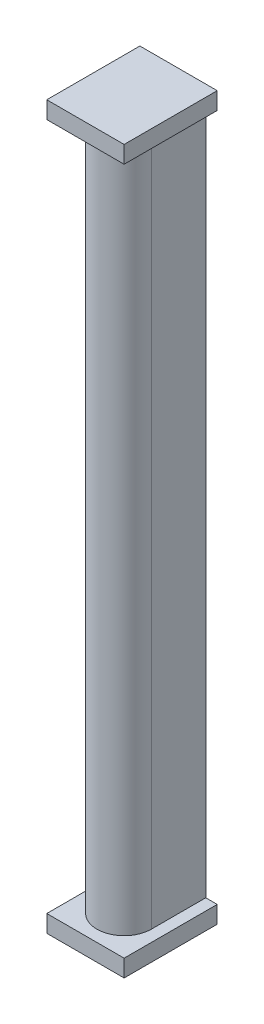
SolidWorks part; units mm, degrees
ref_plane "Front Plane" through (0, 0, 0) normal (0, 0, 1) x (1, 0, 0)
ref_plane "Top Plane" through (0, 0, 0) normal (0, 1, 0) x (1, 0, 0)
ref_plane "Right Plane" through (0, 0, 0) normal (1, 0, 0) x (0, 0, -1)
sketch "Sketch5" plane through (0, 0, 0) normal (0, 1, 0) x (1, 0, 0)
  line L1 (0, 0) -> (9.5, 0)
  line L2 (0, 0) -> (0, -9.5)
  line L4 (9.5, 0) -> (9.5, -9.5)
  arc A0 (0, -9.5) -> (9.5, -9.5) centre (4.75, -9.5) ccw
  dimension "D2" = 9.5
  dimension "D1" = 4.75
  dimension "D3" = 9.5
extrude "Boss-Extrude1" add sketch "Sketch5" against normal blind 120
sketch "Sketch8" plane through (0, -120, 0) normal (0, -1, 0) x (1, 0, 0)
  line L0 (0, 0) -> (0, 9.5) construction
  line L1 (-2, 0) -> (11.5, 0)
  line L2 (-2, 0) -> (-2, 16.25)
  line L3 (-2, 16.25) -> (11.5, 16.25)
  line L4 (11.5, 0) -> (11.5, 16.25)
  line L5 (9.5, 9.5) -> (9.5, 0) construction
  arc A0 (9.5, 9.5) -> (0, 9.5) centre (4.75, 9.5) ccw construction
  point P6 (4.75, 14.25)
  dimension "D1" = 2
  dimension "D2" = 2
  dimension "D3" = 2
extrude "Boss-Extrude4" add sketch "Sketch8" along normal blind 3
sketch "Sketch9" plane through (0, 0, 0) normal (0, 1, 0) x (1, 0, 0)
  line L1 (-2, 0) -> (11.5, 0)
  line L2 (-2, 0) -> (-2, -16.25)
  line L3 (-2, -16.25) -> (11.5, -16.25)
  line L4 (11.5, 0) -> (11.5, -16.25)
extrude "Boss-Extrude5" add sketch "Sketch9" along normal blind 3
